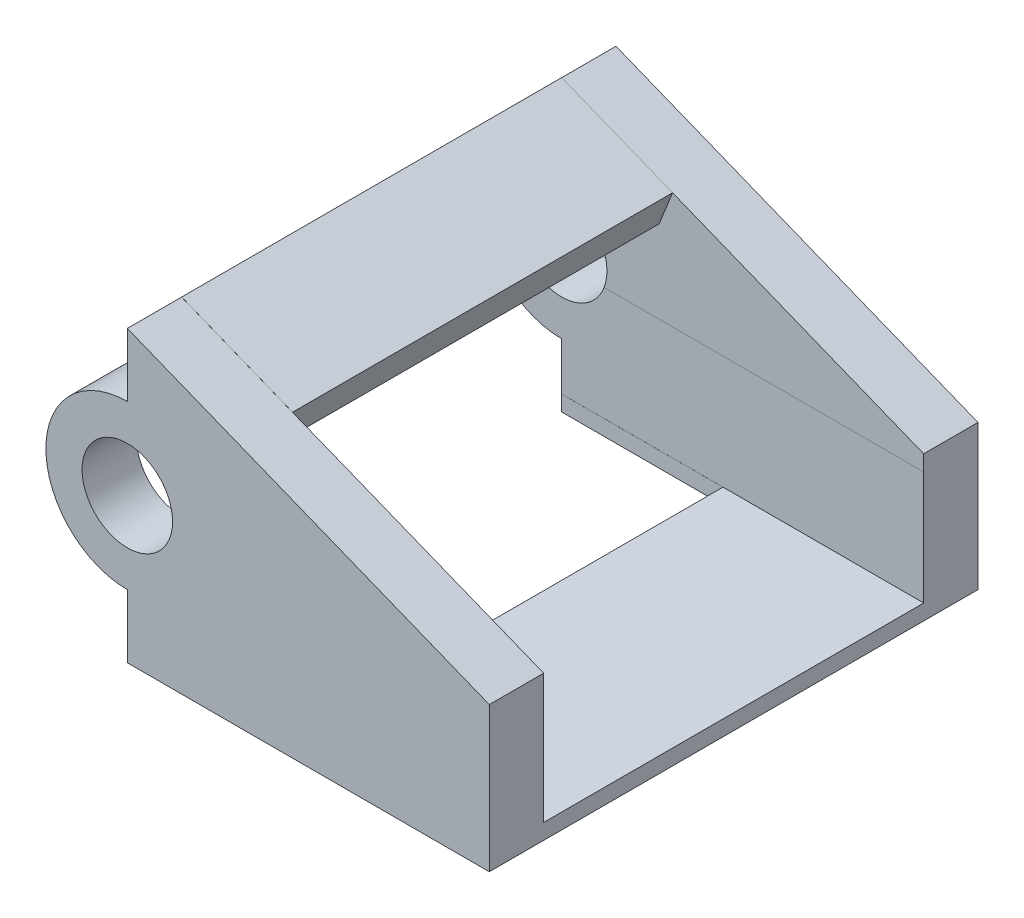
SolidWorks part; units mm, degrees
ref_plane "前视基准面" through (0, 0, 0) normal (0, 0, 1) x (1, 0, 0)
ref_plane "上视基准面" through (0, 0, 0) normal (0, 1, 0) x (1, 0, 0)
ref_plane "右视基准面" through (0, 0, 0) normal (1, 0, 0) x (0, 0, -1)
sketch "草图1" plane through (0, 0, 0) normal (0, 0, 1) x (1, 0, 0)
  line L0 (-8.911, 11.1112) -> (11.089, 3.1112)
  line L6 (-8.911, 11.1112) -> (-8.911, 10.1112)
  line L7 (-8.911, -4.8888) -> (11.089, -4.8888)
  line L8 (11.089, 3.1112) -> (11.089, -4.8888)
  line L9 (-8.911, -3.8888) -> (-8.911, -4.8888)
  line L10 (-8.911, 10.1112) -> (-8.911, 7.6112)
  line L11 (-8.911, -1.3888) -> (-8.911, -3.8888)
  arc A2 (-8.911, 7.6112) -> (-8.911, -1.3888) centre (-8.911, 3.1112) ccw
extrude "凸台-拉伸2" add sketch "草图1" along normal blind 27
sketch "草图8" plane through (0, -4.8888, 0) normal (0, -1, 0) x (-1, 0, 0)
  line L0 (-11.089, -27) -> (-11.089, -18)
  line L1 (-11.089, -27) -> (-11.089, 0) construction
  line L2 (-11.089, 0) -> (-11.089, -3)
  line L3 (8.911, -27) -> (8.911, 0) construction
  line L4 (0, -3) -> (8.911, -3)
  line L5 (-11.089, -3) -> (-11.089, -18)
  line L6 (0, -18) -> (8.911, -18)
  line L7 (8.911, -3) -> (8.911, -18)
  line L8 (0, -3) -> (0, -18)
  line M4 (8.911, -27) -> (8.911, 0)
sketch "草图13" plane through (11.089, 0, 0) normal (1, 0, 0) x (0, 0, -1)
  line L0 (-27, 3.1112) -> (0, 3.1112) construction
  line L1 (-3, -4.8888) -> (-18, -4.8888)
  line L2 (-3, -4.8888) -> (-3, 3.1112)
  line L3 (-3, 3.1112) -> (-18, 3.1112)
  line L4 (-18, -4.8888) -> (-18, 3.1112)
  line L8 (-18, -3.6979) -> (-3, -3.6979)
sketch "草图14" plane through (2.6024, 6.5059, 0) normal (0.3714, 0.9285, 0) x (0.9285, -0.3714, 0)
  line L0 (-12.4003, -27) -> (-12.4003, 0) construction
  line L1 (9.1404, -18) -> (-12.4003, -18)
  line L2 (9.1404, -18) -> (9.1404, -3)
  line L3 (9.1404, -3) -> (-12.4003, -3)
  line L4 (-12.4003, -18) -> (-12.4003, -3)
sketch "草图15" plane through (11.089, 0, 0) normal (1, 0, 0) x (0, 0, -1)
  line L0 (-18, 3.1112) -> (-18, -3.7514)
  line L3 (-18, -3.7514) -> (-3.0025, -3.7514)
  line L5 (-3, 3.1112) -> (-3.0025, -3.7514)
sketch "草图19" plane through (11.089, 0, 0) normal (1, 0, 0) x (0, 0, -1)
  line L1 (-18, -4.8888) -> (-3, -4.8888)
  line L2 (-18, -4.0302) -> (-18, 12.2419)
  line L3 (-18, 12.2419) -> (-3, 12.2419)
extrude "切除-拉伸-薄壁1" cut sketch "草图19" against normal blind 30 from vertex at 0 thin
sketch "草图27" plane through (11.089, 0, 0) normal (1, 0, 0) x (0, 0, -1)
  line L0 (-8, -4.0302) -> (-2.9987, -4.0302)
  line L1 (-2.9987, -4.0302) -> (-3, 2.2419)
  line L2 (-3, 2.2419) -> (-8, 2.2419)
  line L3 (-8, 2.2419) -> (-8, -4.0302)
extrude "切除-拉伸3" cut sketch "草图27" against normal blind 30
sketch "草图28" plane through (0, -4.8888, 0) normal (0, -1, 0) x (1, 0, 0)
  line L1 (-8.911, 3) -> (0, 3)
  line L2 (0, 3) -> (0, 18)
  line L3 (0, 18) -> (-8.911, 18)
  line L4 (-8.911, 18) -> (-8.911, 3)
sketch "草图29" plane through (0, -4.8888, 0) normal (0, -1, 0) x (1, 0, 0)
extrude "切除-拉伸4" cut sketch "草图8" against normal blind 30 contours L4 L8 L6 M4
sketch "草图31" plane through (0, 0, 0) normal (0, 0, -1) x (-1, 0, 0)
  circle A1 centre (9.1501, -1.8626) radius 0.0204
  circle A2 centre (13.8707, 2.9304) radius 0.037
sketch "草图36" plane through (0, 0, 0) normal (0, 0, -1) x (-1, 0, 0)
  circle A0 centre (8.911, 3.1112) radius 2.5
sketch "草图38" plane through (11.089, 0, 0) normal (1, 0, 0) x (0, 0, -1)
  line L0 (-27, 3.1112) -> (-18, 3.1112) construction
  line L1 (-18, -4.0302) -> (-23.9965, -4.0302)
  line L3 (-18, 3.1112) -> (-23.9965, 3.1112)
  line L7 (-23.9965, -4.0302) -> (-23.9965, 11.8065)
  line L8 (-23.9965, 11.8065) -> (-18, 11.8065)
  line L9 (-18, -4.0302) -> (-18, 11.8065)
extrude "切除-拉伸5" cut sketch "草图38" against normal blind 40
ref_plane "基准面8" through (21.089, 0, 0) normal (1, 0, 0) x (0, 0, -1)
sketch "草图41" plane through (21.089, 0, 0) normal (1, 0, 0) x (0, 0, -1)
  line L1 (-23.9965, -4.0302) -> (-17.9965, -4.0302)
  line L2 (-23.9965, -4.0302) -> (-23.9965, 12.9051)
  line L3 (-23.9965, 12.9051) -> (-17.9965, 12.9051)
  line L4 (-17.9965, -4.0302) -> (-17.9965, 12.9051)
extrude "切除-拉伸6" cut sketch "草图41" against normal blind 40
sketch "草图43" plane through (0, -4.8888, 0) normal (0, -1, 0) x (1, 0, 0)
  line L0 (-8.911, 27) -> (-8.911, 18) construction
  line L1 (0, 18) -> (-8.911, 18)
  line L2 (0, 18) -> (0, 24)
  line L3 (0, 24) -> (-8.911, 24)
  line L4 (-8.911, 18) -> (-8.911, 24)
extrude "切除-拉伸7" cut sketch "草图43" against normal blind 40
extrude "切除-拉伸8" cut sketch "草图36" against normal blind 40
sketch "草图45" plane through (2.6024, 6.5059, 0) normal (0.3714, 0.9285, 0) x (0.9285, -0.3714, 0)
  line L0 (-12.4003, -24) -> (-12.4003, -3)
  line L2 (-2.8028, -23.9965) -> (-12.4003, -23.9965)
  line L3 (-2.8028, -23.9965) -> (-2.8028, -3)
  line L4 (-2.8028, -3) -> (-12.4003, -3)
  line L5 (-12.4003, -23.9965) -> (-12.4003, -3)
extrude "凸台-拉伸8" add sketch "草图45" against normal blind 2 separate body contours L3 L4 L0 L2
ref_plane "基准面9" through (-8.911, 5.6112, 23.9965) normal (1, 0, 0) x (0, 0, -1)
sketch "草图47" plane through (0, 0, 3) normal (0, 0, -1) x (-1, 0, 0)
  line L0 (8.911, 11.1112) -> (8.911, 8.9572)
  line L1 (0.7428, 5.6899) -> (9.6538, 9.2543) construction
  line L2 (8.911, 8.9572) -> (9.6538, 9.2543)
  line L3 (9.6538, 9.2543) -> (8.911, 11.1112)
extrude "切除-拉伸10" cut sketch "草图47" against normal blind 25 contours L0 L2 L3
sketch "草图49" plane through (2.6024, 6.5059, 0) normal (0.3714, 0.9285, 0) x (0.9285, -0.3714, 0)
  line L0 (-2.8028, -23.9965) -> (-12.4003, -23.9965) construction
  line L1 (-2.8028, -3) -> (-5.8028, -3)
  line L2 (-2.8028, -3) -> (-2.8028, -23.9965)
  line L3 (-2.8028, -23.9965) -> (-5.8028, -23.9965)
  line L4 (-5.8028, -3) -> (-5.8028, -23.9965)
extrude "切除-拉伸11" cut sketch "草图49" against normal blind 10
